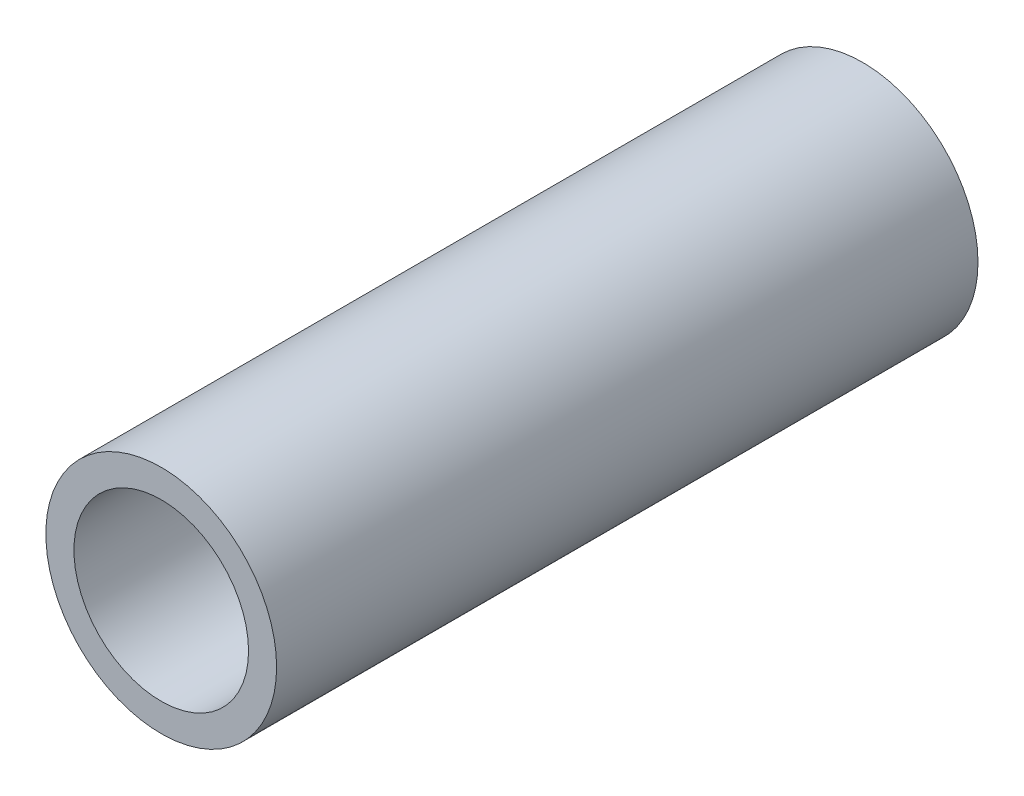
SolidWorks part; units mm, degrees
ref_plane "Front Plane" through (0, 0, 0) normal (0, 0, 1) x (1, 0, 0)
ref_plane "Top Plane" through (0, 0, 0) normal (0, 1, 0) x (1, 0, 0)
ref_plane "Right Plane" through (0, 0, 0) normal (1, 0, 0) x (0, 0, -1)
sketch "Sketch1" plane through (0, 0, 0) normal (0, 0, 1) x (1, 0, 0)
  circle A0 centre (0, 0) radius 12.45
  circle A1 centre (0, 0) radius 16.45
  dimension "D1" = 24.9
  dimension "D2" = 4
extrude "Boss-Extrude1" add sketch "Sketch1" along normal mid plane 100
equation "\"motorWidth\"= 24.9"
equation "\"D1@Sketch1\"=\"motorWidth\""
